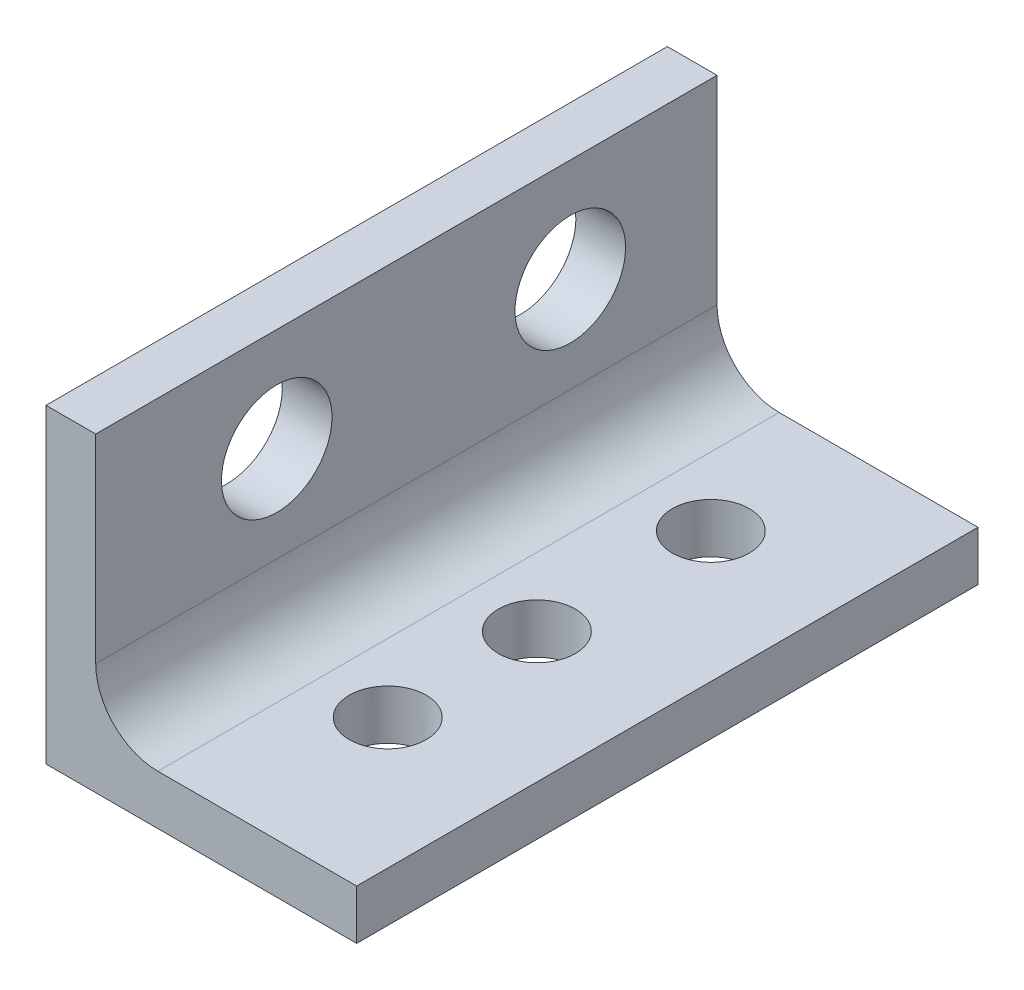
SolidWorks part; units mm, degrees
ref_plane "Front Plane" through (0, 0, 0) normal (0, 0, 1) x (1, 0, 0)
ref_plane "Top Plane" through (0, 0, 0) normal (0, 1, 0) x (1, 0, 0)
ref_plane "Right Plane" through (0, 0, 0) normal (1, 0, 0) x (0, 0, -1)
sketch "Sketch1" plane through (0, 0, 0) normal (0, 0, 1) x (1, 0, 0)
  line L0 (-6.35, 6.35) -> (-6.35, 0)
  line L1 (-6.35, 0) -> (0, 0)
  line L2 (-5.334, 6.35) -> (-5.334, 1.016)
  line L3 (-5.334, 1.016) -> (0, 1.016)
  line L4 (-5.334, 6.35) -> (-6.35, 6.35)
  line L5 (0, 1.016) -> (0, 0)
  dimension "D1" = 6.35
  dimension "D2" = 6.35
  dimension "D3" = 1.016
extrude "Boss-Extrude1" add sketch "Sketch1" along normal blind 12.7
sketch "Sketch3" plane through (0, 1.016, 0) normal (0, 1, 0) x (1, 0, 0)
  line L0 (-2.667, 0) -> (-2.667, -12.7) construction
  line L1 (0, 0) -> (-5.334, 0) construction
  line L3 (0, -12.7) -> (-5.334, -12.7) construction
  line L4 (0, -6.35) -> (-5.334, -6.35) construction
  line L5 (0, -12.7) -> (0, 0) construction
  line L6 (-5.334, -12.7) -> (-5.334, 0) construction
  circle A1 centre (-2.667, -6.35) radius 0.7874
  circle A3 centre (-2.667, -9.398) radius 0.7874
  circle A4 centre (-2.667, -2.794) radius 0.7874
extrude "Cut-Extrude1" cut sketch "Sketch3" against normal blind 2.54
fillet "Fillet1" radius 1.27 1 edges at (-5.334, 1.016, 6.35)
sketch "Sketch4" plane through (-5.334, 0, 0) normal (1, 0, 0) x (0, 0, -1)
  line L0 (-12.7, 0) -> (0, 0) construction
  line L1 (0, 2.286) -> (0, 6.35) construction
  line L5 (-9, 4.24) -> (0.0701, 4.24) construction
  circle A0 centre (-9, 4.24) radius 1.1303
  circle A1 centre (-3, 4.24) radius 1.1303
  dimension "D1" = 4.24
  dimension "D2" = 2.2606
  dimension "D4" = 6
  dimension "D3" = 3
extrude "Cut-Extrude2" cut sketch "Sketch4" against normal up to next
